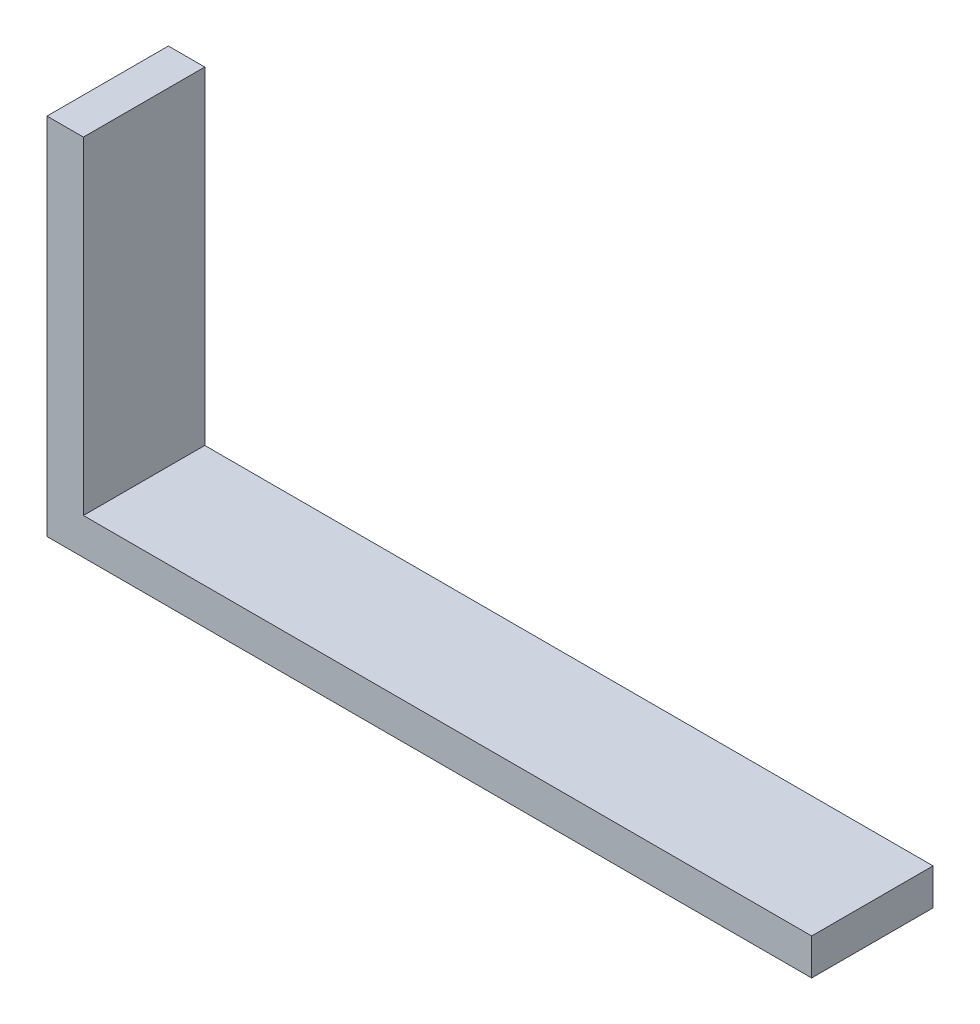
SolidWorks part; units mm, degrees
ref_plane "Front Plane" through (0, 0, 0) normal (0, 0, 1) x (1, 0, 0)
ref_plane "Top Plane" through (0, 0, 0) normal (0, 1, 0) x (1, 0, 0)
ref_plane "Right Plane" through (0, 0, 0) normal (1, 0, 0) x (0, 0, -1)
sketch "Sketch1" plane through (0, 0, 0) normal (0, 0, 1) x (1, 0, 0)
  line L0 (0, 0) -> (0, 30)
  line L1 (0, 30) -> (3, 30)
  line L2 (3, 30) -> (3, 3)
  line L3 (3, 3) -> (63, 3)
  line L4 (63, 3) -> (63, 0)
  line L5 (63, 0) -> (0, 0)
  dimension "D1" = 30
  dimension "D2" = 3
  dimension "D3" = 3
  dimension "D4" = 60
extrude "Boss-Extrude1" add sketch "Sketch1" along normal blind 10
